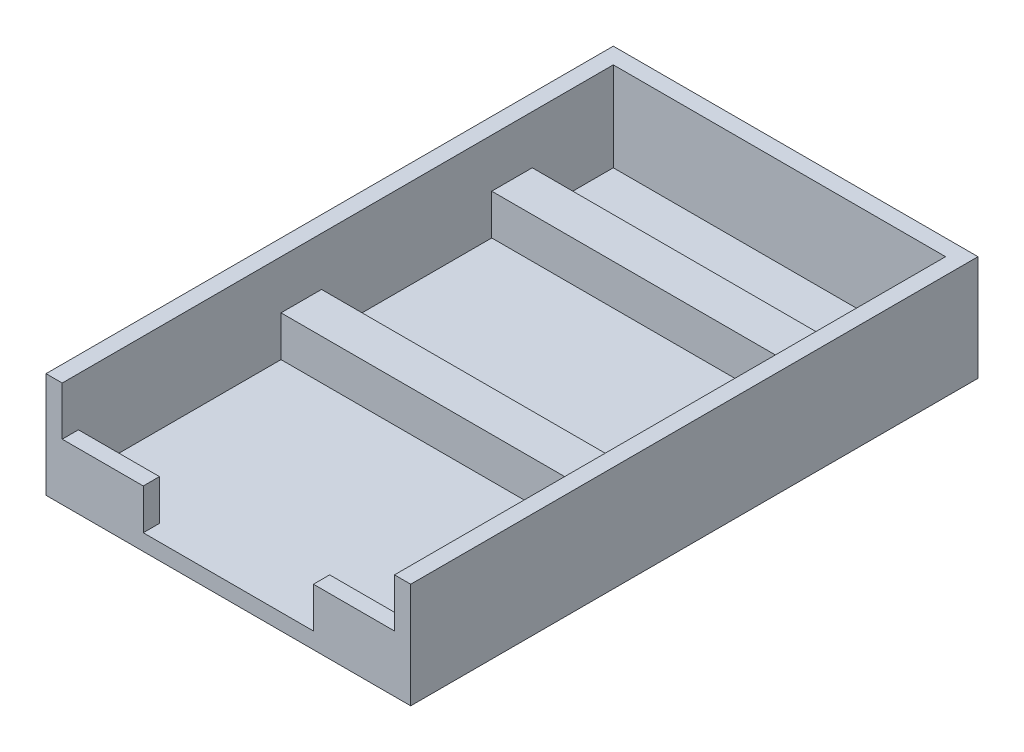
SolidWorks part; units mm, degrees
ref_plane "Front Plane" through (0, 0, 0) normal (0, 0, 1) x (1, 0, 0)
ref_plane "Top Plane" through (0, 0, 0) normal (0, 1, 0) x (1, 0, 0)
ref_plane "Right Plane" through (0, 0, 0) normal (1, 0, 0) x (0, 0, -1)
sketch "Sketch1" plane through (0, 0, 0) normal (0, 1, 0) x (1, 0, 0)
  line L1 (-22.5, 35) -> (22.5, 35)
  line L2 (-22.5, 35) -> (-22.5, -35)
  line L3 (-22.5, -35) -> (22.5, -35)
  line L4 (22.5, 35) -> (22.5, -35)
  line L5 (-22.5, 35) -> (22.5, -35) construction
  line L6 (-22.5, -35) -> (22.5, 35) construction
  point P0 (0, 0)
  dimension "D1" = 70
  dimension "D2" = 45
extrude "Boss-Extrude1" add sketch "Sketch1" along normal blind 10 contours L2 L1 L4 L3
sketch "Sketch2" plane through (0, 10, 0) normal (0, 1, 0) x (1, 0, 0)
  line L1 (-20.5, 33) -> (20.5, 33)
  line L2 (-20.5, 33) -> (-20.5, -33)
  line L3 (-20.5, -33) -> (20.5, -33)
  line L4 (20.5, 33) -> (20.5, -33)
  line L5 (-20.5, 33) -> (20.5, -33) construction
  line L6 (-20.5, -33) -> (20.5, 33) construction
  point P1 (0, 0)
  dimension "D1" = 66
  dimension "D2" = 41
extrude "Cut-Extrude1" cut sketch "Sketch2" against normal blind 8
sketch "Sketch7" plane through (0, 0, 33) normal (0, 0, -1) x (-1, 0, 0)
  line L0 (-20.5, 2) -> (-20.5, 7)
  line L1 (-20.5, 2) -> (-20.5, 10) construction
  line L2 (20.5, 2) -> (20.5, 10) construction
  line L3 (-20.5, 10) -> (20.5, 10)
  line L4 (-20.5, 10) -> (-20.5, 7)
  line L5 (-20.5, 7) -> (20.5, 7)
  line L6 (20.5, 10) -> (20.5, 7)
  line M2 (20.5, 10) -> (-20.5, 10)
  line M3 (-20.5, 10) -> (-20.5, 2)
  line M5 (20.5, 2) -> (20.5, 10)
  dimension "D1" = 5
extrude "Cut-Extrude2" cut sketch "Sketch7" against normal blind 81 and the other way blind 1 contours L5 M3 M5 M2
sketch "Sketch8" plane through (0, 0, 33) normal (0, 0, -1) x (-1, 0, 0)
  line L0 (-20.5, 2) -> (-10.5, 2)
  line L1 (20.5, 2) -> (-20.5, 2) construction
  line L2 (20.5, 2) -> (10.5, 2)
  line L3 (-20.5, 7) -> (20.5, 7) construction
  line L4 (10.5, 2) -> (-10.5, 2)
  line L5 (10.5, 2) -> (10.5, 7)
  line L6 (10.5, 7) -> (-10.5, 7)
  line L7 (-10.5, 2) -> (-10.5, 7)
  line M3 (20.5, 7) -> (-20.5, 7)
  line M5 (-20.5, 2) -> (20.5, 2)
  dimension "D1" = 10
  dimension "D2" = 10
extrude "Cut-Extrude3" cut sketch "Sketch8" against normal blind 42 contours L7 L5 M5 M3
sketch "Sketch9" plane through (0, 2, 0) normal (0, 1, 0) x (1, 0, 0)
  line L0 (-20.5, -33) -> (-20.5, -8)
  line L1 (-20.5, 33) -> (-20.5, -35) construction
  line L2 (20.5, -35) -> (20.5, 33) construction
  line L3 (-20.5, -8) -> (20.5, -8)
  line L4 (-20.5, -8) -> (-20.5, -3)
  line L5 (-20.5, -3) -> (20.5, -3)
  line L6 (20.5, -8) -> (20.5, -3)
  line M6 (20.5, -33) -> (20.5, 33)
  line M8 (-20.5, 33) -> (-20.5, -33)
  dimension "D1" = 25
  dimension "D2" = 5
extrude "Boss-Extrude3" add sketch "Sketch9" along normal blind 5 contours L5 L3 M8 M6
sketch "Sketch10" plane through (0, 2, 0) normal (0, 1, 0) x (1, 0, 0)
  line L0 (-20.5, 33) -> (-20.5, 23)
  line L1 (-20.5, 33) -> (-20.5, -3) construction
  line L2 (20.5, -3) -> (20.5, 33) construction
  line L3 (-20.5, 23) -> (20.5, 23)
  line L4 (-20.5, 23) -> (-20.5, 18)
  line L5 (-20.5, 18) -> (20.5, 18)
  line L6 (20.5, 23) -> (20.5, 18)
  dimension "D1" = 10
  dimension "D2" = 5
extrude "Boss-Extrude4" add sketch "Sketch10" along normal blind 5 contours L6 L3 L4 L5
sketch "Sketch13" plane through (0, 10, 0) normal (0, 1, 0) x (1, 0, 0)
  line L1 (-22.5, 35) -> (-20.5, 35)
  line L2 (-22.5, 35) -> (-22.5, -35)
  line L3 (-22.5, -35) -> (-20.5, -35)
  line L4 (-20.5, 35) -> (-20.5, -35)
extrude "Boss-Extrude5" add sketch "Sketch13" along normal blind 3
sketch "Sketch14" plane through (0, 10, 0) normal (0, 1, 0) x (1, 0, 0)
  line L1 (-20.5, 35) -> (20.5, 35)
  line L2 (-20.5, 35) -> (-20.5, 33)
  line L3 (-20.5, 33) -> (20.5, 33)
  line L4 (20.5, 35) -> (20.5, 33)
extrude "Boss-Extrude6" add sketch "Sketch14" along normal blind 3
sketch "Sketch15" plane through (0, 10, 0) normal (0, 1, 0) x (1, 0, 0)
  line L1 (20.5, 35) -> (22.5, 35)
  line L2 (20.5, 35) -> (20.5, -35)
  line L3 (20.5, -35) -> (22.5, -35)
  line L4 (22.5, 35) -> (22.5, -35)
extrude "Boss-Extrude7" add sketch "Sketch15" along normal blind 3
